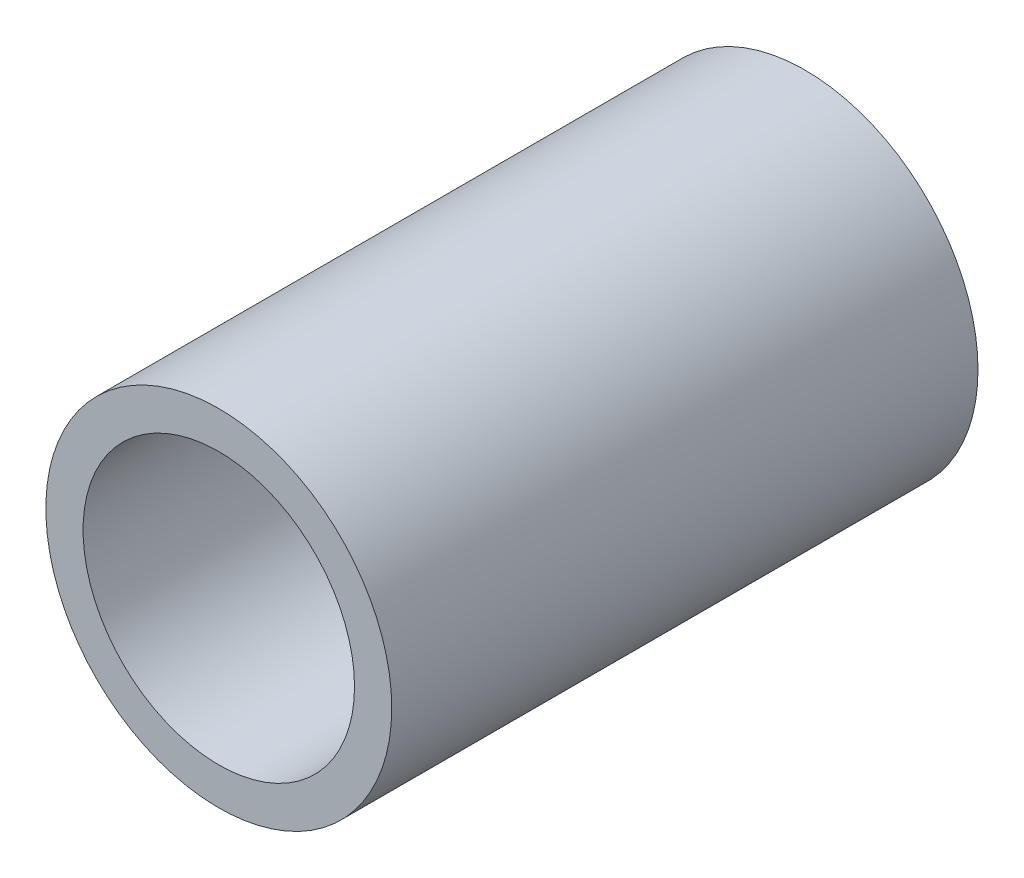
SolidWorks part; units mm, degrees
material "PVC 0.007 Plasticized"
ref_plane "Front Plane" through (0, 0, 0) normal (0, 0, 1) x (1, 0, 0)
ref_plane "Top Plane" through (0, 0, 0) normal (0, 1, 0) x (1, 0, 0)
ref_plane "Right Plane" through (0, 0, 0) normal (1, 0, 0) x (0, 0, -1)
sketch "Sketch1" plane through (0, 0, 0) normal (0, 0, 1) x (1, 0, 0)
  line L0 (10.4648, 0) -> (13.335, 0) construction
  circle A0 centre (0, 0) radius 13.335 construction
  circle A1 centre (0, 0) radius 10.4648 construction
  dimension "ID" = 20.9296
  dimension "OD" = 26.67
  dimension "Wall Thickness" = 2.8702
sketch "Sketch2" plane through (0, 0, 0) normal (1, 0, 0) x (0, 0, -1)
  line L0 (-762, 0) -> (762, 0) construction
  line L1 (-728.6625, 13.335) -> (-728.6625, -13.335) construction
  line L2 (728.6625, 13.335) -> (728.6625, -13.335) construction
  point P4 (0, 0)
  point P8 (-728.6625, 0)
  point P11 (728.6625, 0)
  dimension "Length" = 1524
  dimension "D1" = 33.3375
  dimension "D2" = 33.3375
  dimension "D3" = 26.67
sketch "Sketch3" plane through (0, 0, 0) normal (0, 0, 1) x (1, 0, 0)
  circle A0 centre (0, 0) radius 13.335
  circle A1 centre (0, 0) radius 13.335 construction
  circle A2 centre (0, 0) radius 10.4648 construction
  circle A3 centre (0, 0) radius 10.4648
extrude "Boss-Extrude1" add sketch "Sketch3" along normal up to vertex (762 mm away) and the other way up to vertex (762 mm away) up to point (0, 0, 762) other way up to point (0, 0, -762)
sketch "Sketch4" plane through (0, 0, 762) normal (0, 0, 1) x (1, 0, 0)
  circle A0 centre (0, 0) radius 10.4648 construction
  circle A1 centre (0, 0) radius 13.335 construction
  circle A2 centre (0, 0) radius 10.4648
  circle A3 centre (0, 0) radius 13.335
extrude "Cut-Extrude2" cut sketch "Sketch4" against normal offset from surface (1478.7969 mm away) 45.2031 contours A3 up to face at (10.4648, 0, -762)
equation "\"D1@Sketch2\"=\"OD@Sketch1\" * 1.25"
equation "\"D2@Sketch2\"=\"D1@Sketch2\""
equation "\"D3@Sketch2\"= \"OD@Sketch1\""
